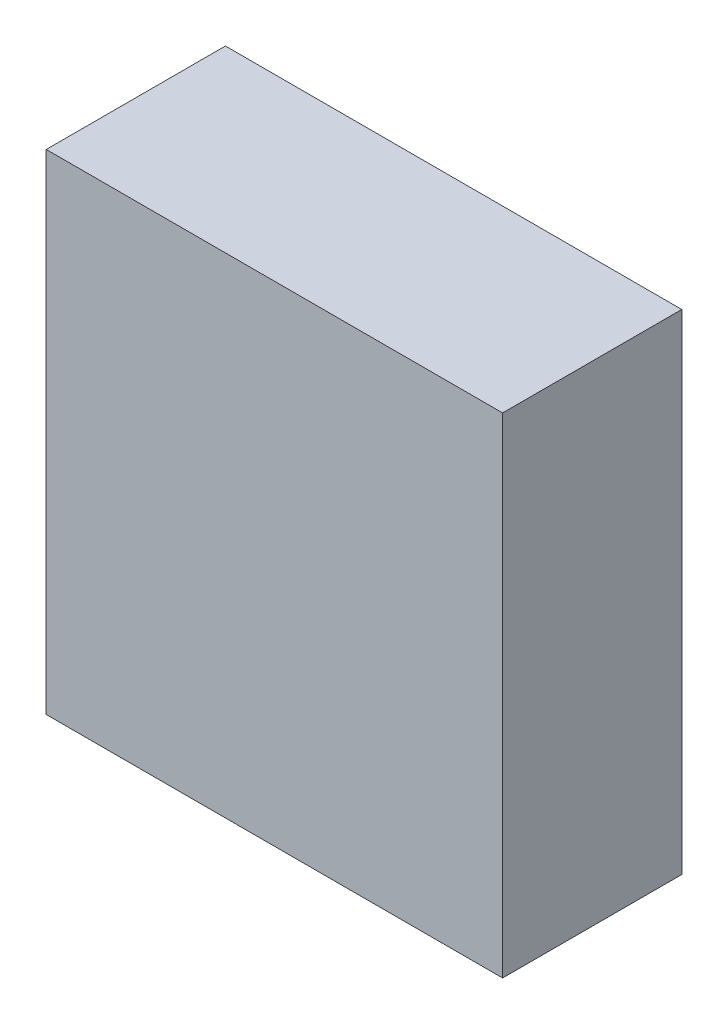
SolidWorks part; units mm, degrees
ref_plane "正面" through (0, 0, 0) normal (1, 0, 0) x (0, 1, 0)
ref_plane "平面" through (0, 0, 0) normal (0, 0, 1) x (0, 1, 0)
ref_plane "右側面" through (0, 0, 0) normal (0, 1, 0) x (-1, 0, 0)
sketch "ｽｹｯﾁ1" plane through (0, 0, 0) normal (0, 0, 1) x (0, 1, 0)
  line L1 (0, 0) -> (87.4, 0)
  line L2 (0, 0) -> (0, 81.5)
  line L3 (0, 81.5) -> (87.4, 81.5)
  line L4 (87.4, 0) -> (87.4, 81.5)
  line L5 (0, 0) -> (87.4, 81.5) construction
  line L6 (0, 81.5) -> (87.4, 0) construction
  point P4 (43.7, 40.75)
  dimension "D1" = 87.4
  dimension "D2" = 81.5
extrude "ﾎﾞｽ - 押し出し1" add sketch "ｽｹｯﾁ1" along normal blind 32
